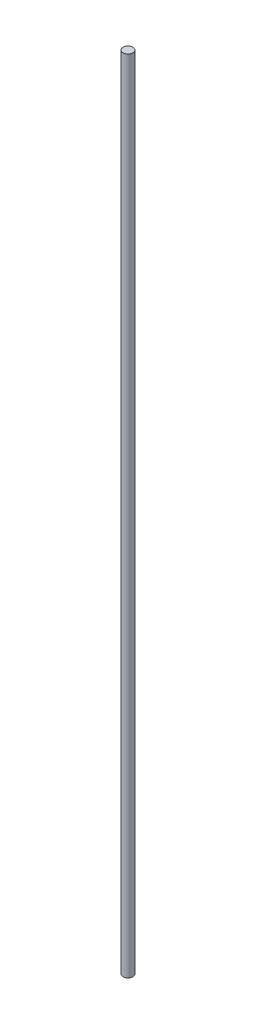
SolidWorks part; units mm, degrees
material "Chrome Stainless Steel"
ref_plane "Front Plane" through (0, 0, 0) normal (0, 0, 1) x (1, 0, 0)
ref_plane "Top Plane" through (0, 0, 0) normal (0, 1, 0) x (1, 0, 0)
ref_plane "Right Plane" through (0, 0, 0) normal (1, 0, 0) x (0, 0, -1)
sketch "Sketch1" plane through (0, 0, 0) normal (0, 1, 0) x (1, 0, 0)
  circle A0 centre (0, 0) radius 4
  dimension "D1" = 8
extrude "Boss-Extrude1" add sketch "Sketch1" along normal blind 650 contours A0
